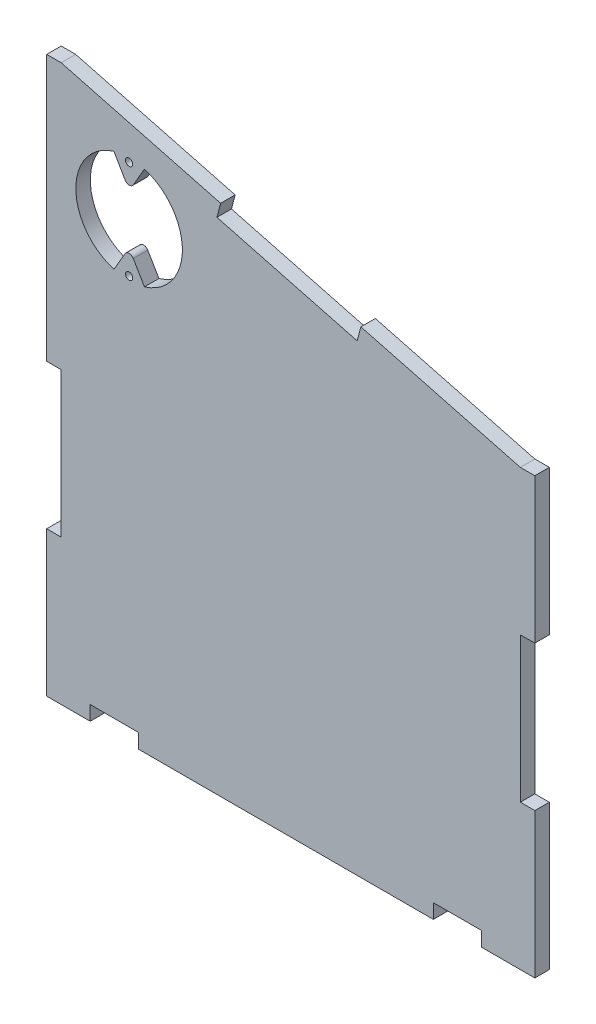
SolidWorks part; units mm, degrees
ref_plane "Front Plane" through (0, 0, 0) normal (0, 0, 1) x (1, 0, 0)
ref_plane "Top Plane" through (0, 0, 0) normal (0, 1, 0) x (1, 0, 0)
ref_plane "Right Plane" through (0, 0, 0) normal (1, 0, 0) x (0, 0, -1)
sketch "Model" plane through (0, 0, 0) normal (0, 0, 1) x (1, 0, 0)
  line L1 (403.6011, 194.9698) -> (403.6011, 164.9698)
  line L2 (316.8563, 227.9025) -> (316.8563, 137.9025) construction
  line L6 (308.6011, 227.9025) -> (308.6011, 249.9698) construction
  line L10 (406.6011, 134.9698) -> (305.6011, 134.9698) construction
  line L15 (305.6011, 194.9698) -> (308.6011, 194.9698)
  line L16 (308.6011, 249.9698) -> (305.6011, 249.9698)
  line L20 (305.6011, 164.9698) -> (308.6011, 164.9698)
  line L21 (308.6011, 194.9698) -> (308.6011, 164.9698)
  line L22 (305.6011, 194.9698) -> (308.6011, 164.9698) construction
  line L23 (305.6011, 164.9698) -> (308.6011, 194.9698) construction
  line L24 (403.6011, 224.9698) -> (370.6072, 233.6524)
  line L26 (402.8376, 222.0685) -> (307.8376, 247.0685) construction
  line L27 (308.6011, 249.9698) -> (307.88, 247.0577) construction
  line L28 (406.6011, 134.9698) -> (395.6011, 134.9698)
  line L30 (356.1011, 237.4698) -> (355.3376, 234.5685) construction
  line L38 (341.595, 241.2872) -> (340.8315, 238.3859)
  line L41 (308.6011, 249.9698) -> (308.6011, 134.9698) construction
  line L62 (395.6011, 134.9698) -> (395.6011, 137.9698)
  line L63 (403.6011, 224.9698) -> (403.6011, 194.9698) construction
  line L64 (370.6072, 233.6524) -> (369.8438, 230.7511)
  line L65 (369.8438, 230.7511) -> (340.8315, 238.3859)
  line L66 (341.595, 241.2872) -> (308.6011, 249.9698)
  line L67 (406.6011, 224.9698) -> (403.6011, 224.9698)
  line L68 (403.6011, 224.9698) -> (308.6011, 249.9698) construction
  line L69 (395.6011, 137.9698) -> (385.6011, 137.9698)
  line L74 (305.6011, 249.9698) -> (305.6011, 194.9698) construction
  line L75 (385.6011, 137.9698) -> (385.6011, 134.9698)
  line L76 (305.6011, 249.9698) -> (305.6011, 194.9698)
  line L77 (305.6011, 164.9698) -> (305.6011, 134.9698)
  line L78 (385.6011, 134.9698) -> (324.6011, 134.9698)
  line L79 (324.6011, 134.9698) -> (324.6011, 137.9698)
  line L80 (324.6011, 137.9698) -> (314.6011, 137.9698)
  line L81 (314.6011, 137.9698) -> (314.6011, 134.9698)
  line L82 (314.6011, 134.9698) -> (305.6011, 134.9698)
  line L83 (322.6524, 243.1514) -> (322.6524, 215.253) construction
  line L84 (336.6016, 228.9819) -> (308.7032, 228.9819) construction
  line L85 (330.2411, 236.977) -> (319.5228, 218.4123) construction
  line L90 (336.2024, 228.9819) -> (331.1024, 228.9819) construction
  line L147 (311.9164, 231.4819) -> (333.4164, 231.4819) construction
  line L148 (311.9164, 231.4819) -> (311.9402, 226.382) construction
  line L149 (311.9402, 226.382) -> (333.3983, 226.5251) construction
  line L150 (333.4164, 231.4819) -> (333.3983, 226.5251) construction
  line L155 (319.5228, 218.4123) -> (315.1002, 220.9522) construction
  line L156 (315.1002, 220.9522) -> (325.8302, 239.5371) construction
  line L157 (325.8302, 239.5371) -> (330.2411, 236.977) construction
  line L158 (319.5228, 239.5515) -> (330.2411, 220.9868) construction
  line L159 (330.2411, 220.9868) -> (325.8302, 218.4267) construction
  line L160 (325.8302, 218.4267) -> (315.1002, 237.0116) construction
  line L161 (315.1002, 237.0116) -> (319.5228, 239.5515) construction
  line L162 (319.5228, 239.5515) -> (321.8146, 235.5819)
  line L163 (323.5467, 235.5819) -> (325.8302, 239.5371)
  line L164 (319.5228, 218.4123) -> (321.7941, 222.3464)
  line L165 (323.5222, 222.3531) -> (325.8302, 218.4267)
  line L335 (406.6011, 224.9698) -> (406.6011, 194.9698)
  line L336 (406.6011, 194.9698) -> (403.6011, 194.9698)
  line L354 (403.6011, 164.9698) -> (406.6011, 164.9698)
  line L355 (406.6011, 164.9698) -> (406.6011, 134.9698)
  circle A2 centre (322.6524, 228.9819) radius 11.0232 construction
  arc A3 (325.8302, 218.4267) -> (325.8302, 239.5371) centre (322.6524, 228.9819) ccw
  arc A4 (319.5228, 239.5515) -> (319.5228, 218.4123) centre (322.6524, 228.9819) ccw
  arc A5 (321.8146, 235.5819) -> (323.5467, 235.5819) centre (322.6807, 236.0819) ccw
  arc A6 (323.5222, 222.3531) -> (321.7941, 222.3464) centre (322.6601, 221.8464) ccw
  circle A7 centre (322.6524, 239.1819) radius 0.75
  circle A8 centre (322.6524, 218.7819) radius 0.75
  point P2 (277.1663, 249.84)
  point P4 (414.3116, 222.6672)
  point P18 (307.1011, 179.9698)
  point P22 (179.0263, 224.9408)
  point P23 (279.0253, 249.9372)
  point P27 (290.9628, 250.114)
  point P29 (227.9628, 225.114)
  point P31 (222.8578, 224.9698)
  point P64 (322.6807, 234.0819)
  point P67 (322.6524, 223.8329)
  point P79 (322.5504, 228.7726)
  point P84 (322.5504, 228.7726)
  point P348 (216.8578, 224.9698)
  dimension "D18" = 5.1
  dimension "D27" = 5.1
  dimension "D25" = 2.5
  dimension "D30" = 1
  dimension "D31" = 1
  dimension "D32" = 20.4
  dimension "D33" = 10.2
  dimension "D3" = 95
  dimension "D4" = 30
  dimension "D5" = 3
  dimension "D6" = 3
  dimension "D7" = 3
  dimension "D8" = 3
  dimension "D9" = 30
  dimension "D10" = 30
  dimension "D11" = 10
  dimension "D12" = 10
  dimension "D13" = 11
  dimension "D14" = 3
  dimension "D15" = 9
  dimension "D16" = 15
  dimension "D17" = 15
  dimension "D19" = 3
  dimension "D20" = 115
  dimension "D21" = 21.5
  dimension "D22" = 30
  dimension "D23" = 30
  dimension "D24" = 3
  dimension "D26" = 5.1
  dimension "D28" = 60
  dimension "D29" = 60
extrude "Boss-Extrude1" add sketch "Model" along normal blind 3
